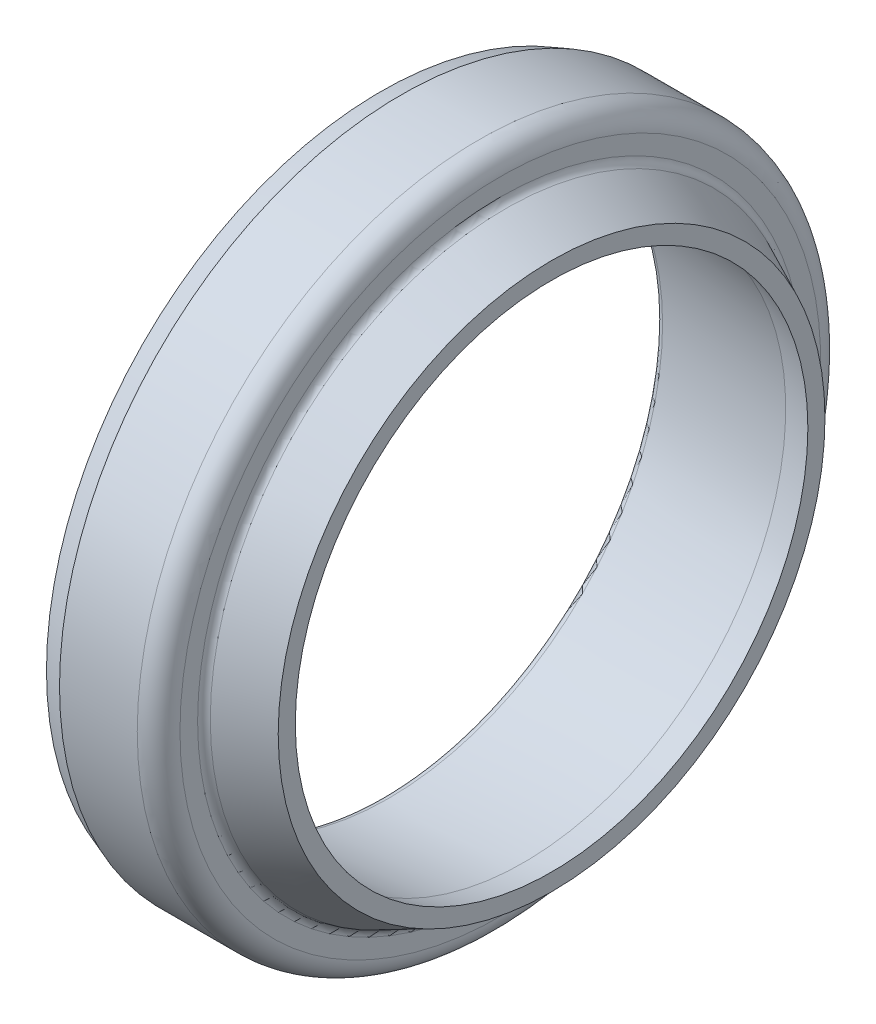
SolidWorks part; units mm, degrees
material "Rubber"
ref_plane "Front" through (0, 0, 0) normal (0, 0, 1) x (1, 0, 0)
ref_plane "Top" through (0, 0, 0) normal (0, 1, 0) x (1, 0, 0)
ref_plane "Right" through (0, 0, 0) normal (1, 0, 0) x (0, 0, -1)
curve "ImportedCurve1"
curve "ImportedCurve2"
curve "ImportedCurve3"
curve "ImportedCurve4"
curve "ImportedCurve5"
curve "ImportedCurve6"
curve "ImportedCurve7"
curve "ImportedCurve8"
curve "ImportedCurve9"
curve "ImportedCurve10"
curve "ImportedCurve11"
curve "ImportedCurve12"
curve "ImportedCurve13"
curve "ImportedCurve14"
curve "ImportedCurve15"
curve "ImportedCurve16"
curve "ImportedCurve17"
curve "ImportedCurve18"
curve "ImportedCurve19"
curve "ImportedCurve20"
curve "ImportedCurve21"
curve "ImportedCurve22"
curve "ImportedCurve23"
curve "ImportedCurve24"
curve "ImportedCurve25"
curve "ImportedCurve26"
curve "ImportedCurve27"
curve "ImportedCurve28"
curve "ImportedCurve29"
curve "ImportedCurve30"
curve "ImportedCurve31"
curve "ImportedCurve32"
curve "ImportedCurve33"
curve "ImportedCurve34"
curve "ImportedCurve35"
curve "ImportedCurve36"
curve "ImportedCurve37"
curve "ImportedCurve38"
curve "ImportedCurve39"
curve "ImportedCurve40"
curve "ImportedCurve41"
curve "ImportedCurve42"
curve "ImportedCurve43"
curve "ImportedCurve44"
sketch "Sketch1" plane through (0, 0, 0) normal (0, 0, 1) x (1, 0, 0)
  line L0 (577.0617, 423.227) -> (577.0617, 420.516) construction
  line L1 (577.5181, 420.0179) -> (585.415, 419.327) construction
  line L2 (585.415, 419.327) -> (587.0617, 418.977) construction
  line L3 (587.0617, 418.977) -> (587.0617, 419.977) construction
  line L4 (584.3504, 421.2413) -> (587.0617, 419.977) construction
  line L5 (584.0617, 422.727) -> (584.0617, 421.6944) construction
  line L6 (578.2617, 423.977) -> (582.8117, 423.977) construction
  line L7 (578.2617, 423.977) -> (577.0617, 423.5402) construction
  line L8 (577.0617, 423.227) -> (577.0617, 420.516)
  line L9 (577.5181, 420.0179) -> (585.415, 419.327)
  line L10 (585.415, 419.327) -> (587.0617, 418.977)
  line L11 (587.0617, 418.977) -> (587.0617, 419.977)
  line L12 (584.3504, 421.2413) -> (587.0617, 419.977)
  line L13 (584.0617, 422.727) -> (584.0617, 421.6944)
  line L14 (578.2617, 423.977) -> (582.8117, 423.977)
  line L15 (578.2617, 423.977) -> (577.0617, 423.5402)
  line L16 (577.0617, 403.977) -> (591.3144, 403.977) construction
  line L17 (577.0617, 404.977) -> (577.0617, 402.977) construction
  line L18 (577.0617, 423.5402) -> (577.0617, 423.227)
  spline S0 degree 3 poles (577.0617, 420.516) (577.0617, 420.243) (577.2461, 420.0417) (577.5181, 420.0179) knots 0 0 0 0 1 1 1 1 weights 1 0.824852 0.824852 1 construction
  spline S1 degree 3 poles (584.0617, 421.6944) (584.0617, 421.4945) (584.1691, 421.3258) (584.3504, 421.2413) knots 0 0 0 0 1 1 1 1 weights 1 0.895594 0.895594 1 construction
  spline S2 degree 3 poles (584.0617, 422.727) (584.0617, 423.4592) (583.5439, 423.977) (582.8117, 423.977) knots 0 0 0 0 1 1 1 1 weights 1 0.804738 0.804738 1 construction
  spline S3 degree 3 poles (577.0617, 420.516) (577.0617, 420.243) (577.2461, 420.0417) (577.5181, 420.0179) knots 0 0 0 0 1 1 1 1 weights 1 0.824852 0.824852 1
  spline S4 degree 3 poles (584.0617, 421.6944) (584.0617, 421.4945) (584.1691, 421.3258) (584.3504, 421.2413) knots 0 0 0 0 1 1 1 1 weights 1 0.895594 0.895594 1
  spline S5 degree 3 poles (584.0617, 422.727) (584.0617, 423.4592) (583.5439, 423.977) (582.8117, 423.977) knots 0 0 0 0 1 1 1 1 weights 1 0.804738 0.804738 1
  dimension "D1" = 15
revolve "Revolve1" add sketch "Sketch1" angle 360 about L16
